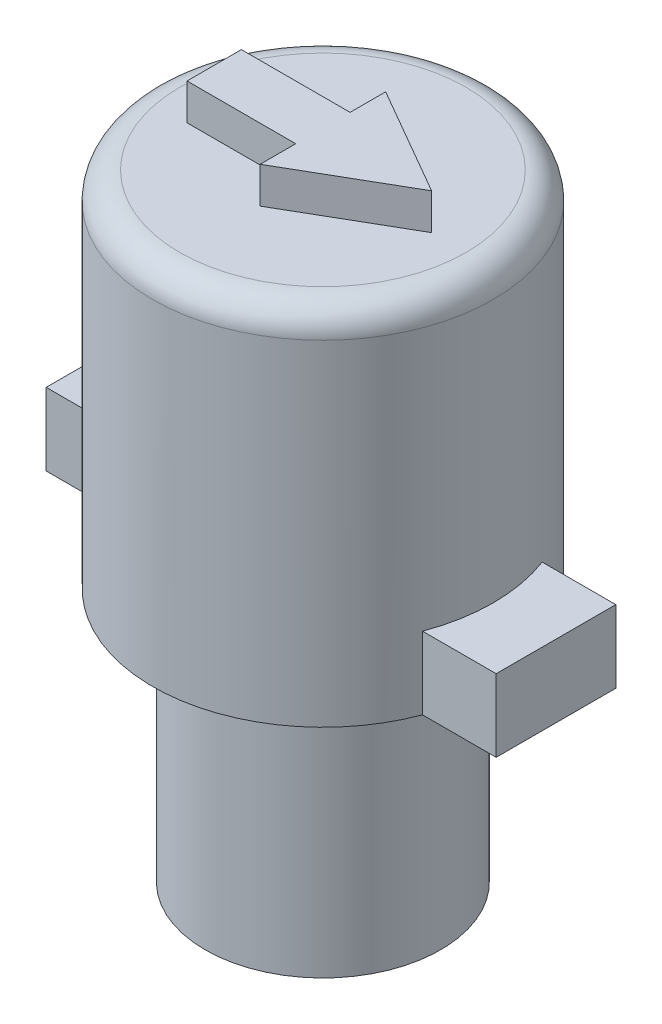
SolidWorks part; units mm, degrees
ref_plane "Front Plane" through (0, 0, 0) normal (0, 0, 1) x (1, 0, 0)
ref_plane "Top Plane" through (0, 0, 0) normal (0, 1, 0) x (1, 0, 0)
ref_plane "Right Plane" through (0, 0, 0) normal (1, 0, 0) x (0, 0, -1)
sketch "Sketch1" plane through (0, 0, 0) normal (0, 1, 0) x (1, 0, 0)
  circle A0 centre (0, 0) radius 3.25
  dimension "D1" = 6.5
extrude "Boss-Extrude1" add sketch "Sketch1" along normal blind 7.018 contours A0
sketch "Sketch2" plane through (0, 0, 0) normal (0, -1, 0) x (1, 0, 0)
  circle A1 centre (0, 0) radius 1.75
  dimension "D1" = 3.5
extrude "Cut-Extrude1" [suppressed] cut sketch "Sketch2" against normal blind 2.5
sketch "Sketch6" plane through (0, 7.018, 0) normal (0, 1, 0) x (1, 0, 0)
  circle A0 centre (0, 0) radius 4.7
  dimension "D1" = 9.4
extrude "Boss-Extrude2" add sketch "Sketch6" along normal blind 10 contours A0
fillet "Fillet1" radius 0.75 1 edges at (0, 17.018, 4.7)
sketch "Sketch7" plane through (0, 17.018, 0) normal (0, 1, 0) x (1, 0, 0)
  line L0 (0, 0) -> (-3, 0) construction
  line L1 (0, 0) -> (1, 0) construction
  line L2 (0, 0) -> (1, 0) construction
  line L3 (3, 0) -> (0, 1.7321)
  line L4 (0, 1.7321) -> (0, -1.7321)
  line L5 (0, -1.7321) -> (3, 0)
  line L6 (1, 0) -> (3, 0) construction
  line L7 (-3, 0) -> (-3, 0.75)
  line L8 (-3, 0.75) -> (0, 0.75)
  line L9 (0, 0.75) -> (0, -0.75)
  line L10 (0, -0.75) -> (-3, -0.75)
  line L11 (-3, -0.75) -> (-3, 0)
  circle A0 centre (1, 0) radius 1 construction
  dimension "D1" = 1
  dimension "D2" = 2
  dimension "D3" = 3
  dimension "D4" = 0.75
  dimension "D5" = 0.75
sketch "Sketch8" plane through (0, 17.018, 0) normal (0, 1, 0) x (1, 0, 0)
  line L0 (0, 0.75) -> (-3, 0.75)
  line L1 (-3, 0.75) -> (-3, -0.75)
  line L2 (-3, -0.75) -> (0, -0.75)
  line L3 (0, -0.75) -> (0, -1.7321)
  line L4 (0, -1.7321) -> (3, 0)
  line L5 (3, 0) -> (0, 1.7321)
  line L6 (0, 1.7321) -> (0, 0.75)
extrude "Boss-Extrude3" add sketch "Sketch8" along normal blind 1
sketch "Sketch9" plane through (0, 7.018, 0) normal (0, -1, 0) x (1, 0, 0)
  line L1 (-4.5889, 1.016) -> (-6.6209, 1.016)
  line L2 (-6.6209, 1.016) -> (-6.6209, -1.016)
  line L3 (-6.6209, -1.016) -> (-4.5889, -1.016)
  line L4 (4.4005, 1.651) -> (6.4325, 1.651)
  line L5 (6.4325, 1.651) -> (6.4325, -1.651)
  line L6 (6.4325, -1.651) -> (4.4005, -1.651)
  arc A0 (-4.5889, 1.016) -> (-4.5889, -1.016) centre (0, 0) ccw
  circle A1 centre (0, 0) radius 4.7
  arc A2 (4.4005, -1.651) -> (4.4005, 1.651) centre (0, 0) ccw
  dimension "D2" = 2.032
  dimension "D3" = 2.032
  dimension "D4" = 3.302
  dimension "D5" = 2.032
  dimension "D1" = 0
extrude "Boss-Extrude4" add sketch "Sketch9" against normal blind 2
